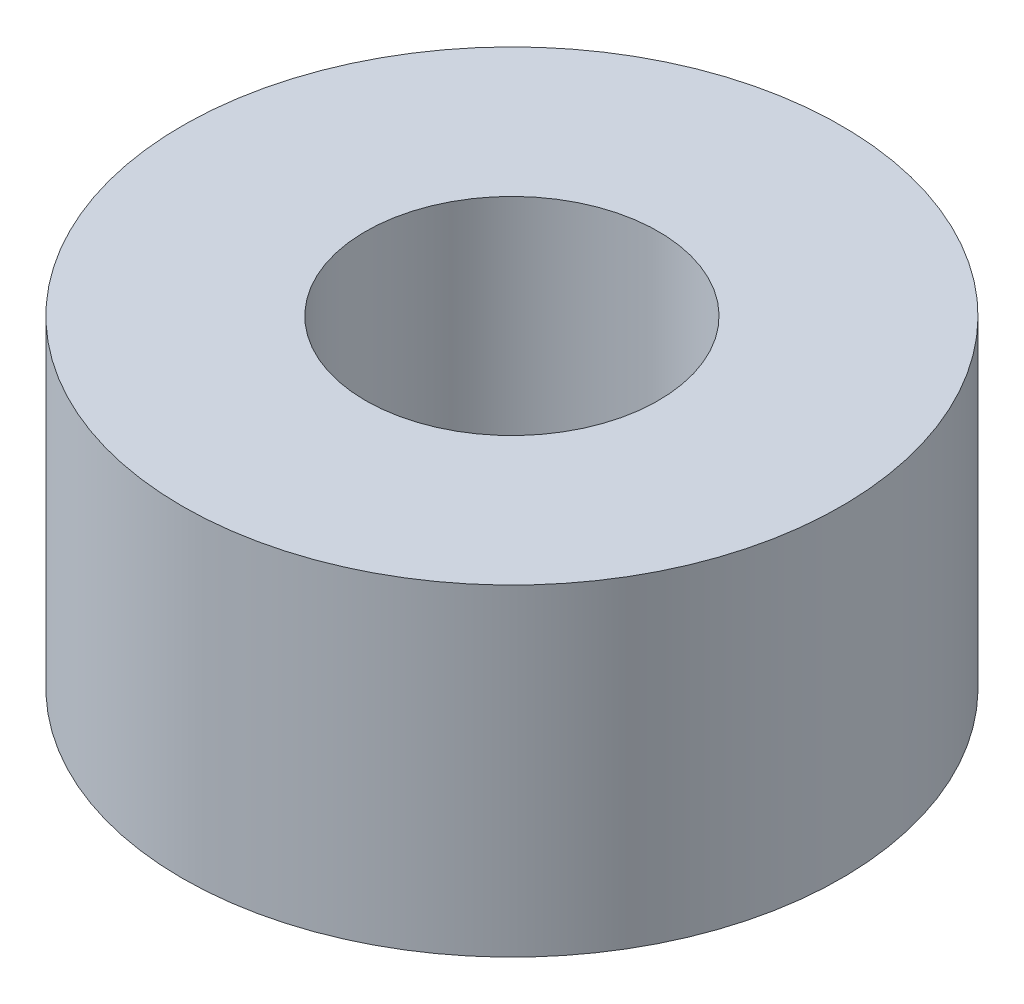
SolidWorks part; units mm, degrees
ref_plane "Front Plane" through (0, 0, 0) normal (0, 0, 1) x (1, 0, 0)
ref_plane "Top Plane" through (0, 0, 0) normal (0, 1, 0) x (1, 0, 0)
ref_plane "Right Plane" through (0, 0, 0) normal (1, 0, 0) x (0, 0, -1)
sketch "Sketch1" plane through (0, 0, 0) normal (0, 1, 0) x (1, 0, 0)
  circle A0 centre (0, 0) radius 2.54
  circle A1 centre (0, 0) radius 5.715
  dimension "D1" = 5.08
  dimension "D2" = 11.43
extrude "Boss-Extrude1" add sketch "Sketch1" along normal blind 5.588
